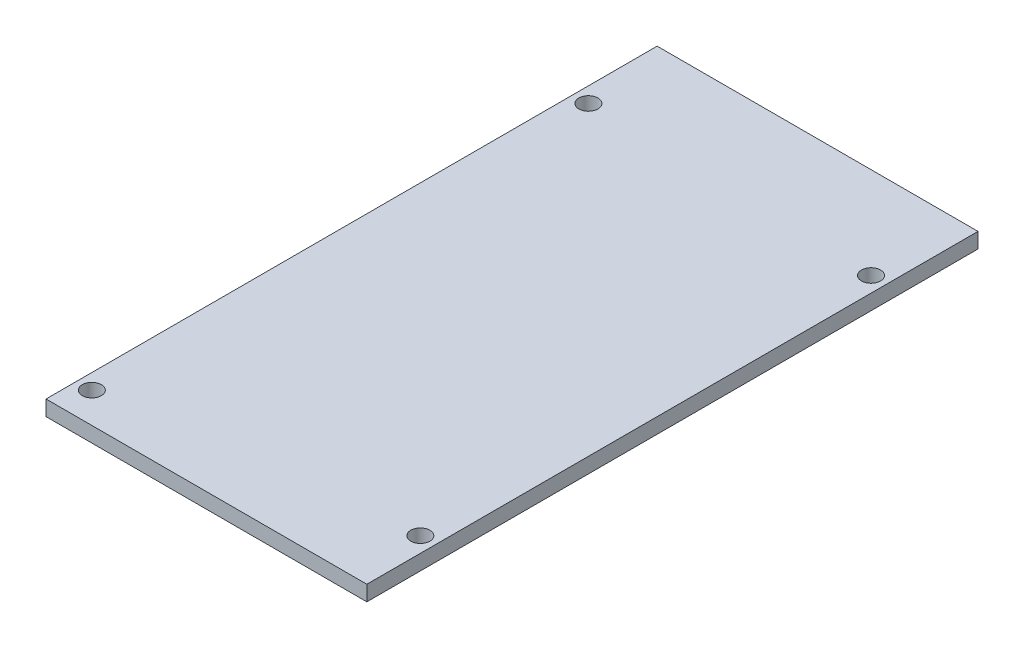
SolidWorks part; units mm, degrees
ref_plane "Front Plane" through (0, 0, 0) normal (0, 0, 1) x (1, 0, 0)
ref_plane "Top Plane" through (0, 0, 0) normal (0, 1, 0) x (1, 0, 0)
ref_plane "Right Plane" through (0, 0, 0) normal (1, 0, 0) x (0, 0, -1)
sketch "Sketch1" plane through (0, 0, 0) normal (0, 1, 0) x (1, 0, 0)
  line L1 (0, 0) -> (53.34, 0)
  line L2 (0, 0) -> (0, 101.6)
  line L3 (0, 101.6) -> (53.34, 101.6)
  line L4 (53.34, 0) -> (53.34, 101.6)
  circle A0 centre (50.8, 86.36) radius 1.5875
  circle A1 centre (2.54, 87.63) radius 1.5875
  circle A2 centre (2.54, 5.08) radius 1.5875
  circle A3 centre (50.8, 11.43) radius 1.5875
  dimension "D4" = 3.175
  dimension "D1" = 53.34
  dimension "D2" = 101.6
  dimension "D3" = 2.54
  dimension "D5" = 13.97
  dimension "D6" = 15.24
  dimension "D7" = 50.8
  dimension "D8" = 2.54
  dimension "D9" = 2.54
  dimension "D10" = 96.52
  dimension "D11" = 90.17
extrude "Boss-Extrude1" add sketch "Sketch1" along normal blind 2.54
